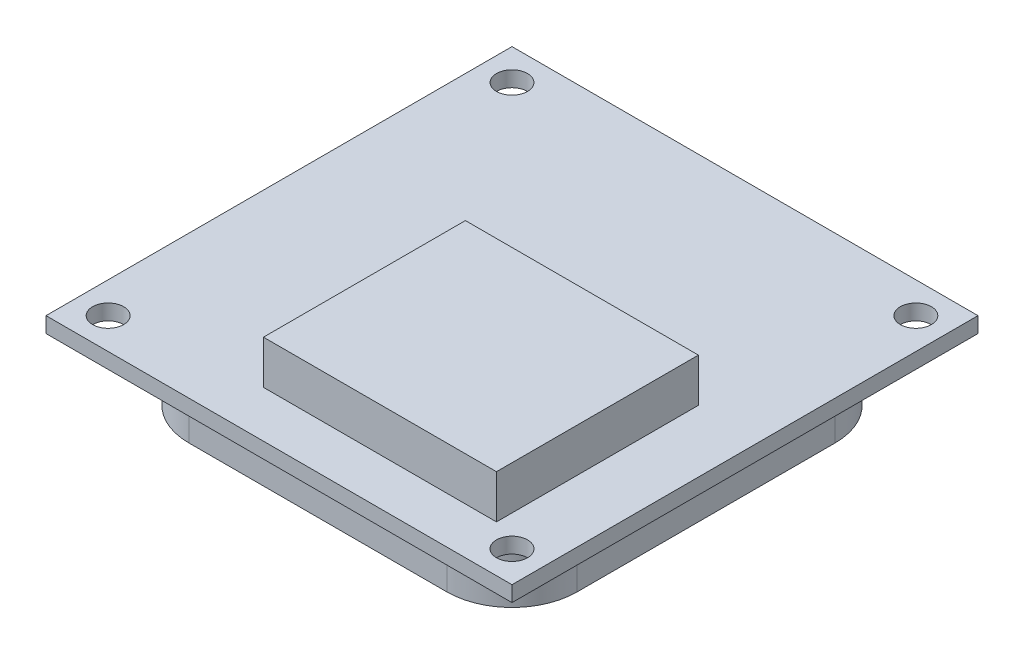
SolidWorks part; units mm, degrees
ref_plane "Front Plane" through (0, 0, 0) normal (0, 0, 1) x (1, 0, 0)
ref_plane "Top Plane" through (0, 0, 0) normal (0, 1, 0) x (1, 0, 0)
ref_plane "Right Plane" through (0, 0, 0) normal (1, 0, 0) x (0, 0, -1)
sketch "Sketch1" plane through (0, 0, 0) normal (0, 1, 0) x (1, 0, 0)
  line L1 (-12.6176, 9.5735) -> (17.3824, 9.5735)
  line L2 (-12.6176, 9.5735) -> (-12.6176, -20.4265)
  line L3 (-12.6176, -20.4265) -> (17.3824, -20.4265)
  line L4 (17.3824, 9.5735) -> (17.3824, -20.4265)
  circle A0 centre (-10.6176, 7.5735) radius 1
  circle A1 centre (15.3824, 7.5735) radius 1
  circle A2 centre (15.3824, -18.4265) radius 1
  circle A3 centre (-10.6176, -18.4265) radius 1
  dimension "D3" = 2
  dimension "D4" = 2
  dimension "D5" = 2
  dimension "D6" = 2
  dimension "D7" = 2
  dimension "D11" = 2
  dimension "D1" = 30
  dimension "D2" = 30
  dimension "D8" = 2
  dimension "D9" = 2
  dimension "D10" = 2
extrude "Boss-Extrude2" add sketch "Sketch1" along normal blind 1
sketch "Sketch2" plane through (0, 1, 0) normal (0, 1, 0) x (1, 0, 0)
  line L0 (-12.6176, -20.4265) -> (17.3824, -20.4265) construction
  line L1 (-1.6176, -4.4265) -> (13.3824, -4.4265)
  line L2 (-1.6176, -4.4265) -> (-1.6176, -17.4265)
  line L3 (-1.6176, -17.4265) -> (13.3824, -17.4265)
  line L4 (13.3824, -4.4265) -> (13.3824, -17.4265)
  line L5 (17.3824, -20.4265) -> (17.3824, 9.5735) construction
  dimension "D1" = 15
  dimension "D2" = 13
  dimension "D3" = 3
  dimension "D4" = 4
extrude "Boss-Extrude3" add sketch "Sketch2" along normal blind 2.8
sketch "Sketch3" plane through (0, 0, 0) normal (0, -1, 0) x (1, 0, 0)
  line L0 (-12.6176, 20.4265) -> (17.3824, 20.4265) construction
  line L1 (-5.9262, 17.9265) -> (10.6909, 17.9265)
  line L2 (-10.1176, 13.735) -> (-10.1176, -2.882)
  line L3 (-5.9262, -7.0735) -> (10.6909, -7.0735)
  line L4 (14.8824, 13.735) -> (14.8824, -2.882)
  line L5 (-12.6176, -9.5735) -> (-12.6176, 20.4265) construction
  arc A0 (10.6909, 17.9265) -> (14.8824, 13.735) centre (10.6909, 13.735) cw
  arc A1 (14.8824, -2.882) -> (10.6909, -7.0735) centre (10.6909, -2.882) cw
  arc A2 (-5.9262, -7.0735) -> (-10.1176, -2.882) centre (-5.9262, -2.882) cw
  arc A3 (-10.1176, 13.735) -> (-5.9262, 17.9265) centre (-5.9262, 13.735) cw
  point P10 (14.8824, 17.9265)
  point P15 (-10.1176, -7.0735)
  point P18 (-10.1176, 17.9265)
  dimension "D5" = 23.5
  dimension "D1" = 25
  dimension "D2" = 25
  dimension "D3" = 2.5
  dimension "D4" = 2.5
extrude "Boss-Extrude4" add sketch "Sketch3" along normal blind 4
